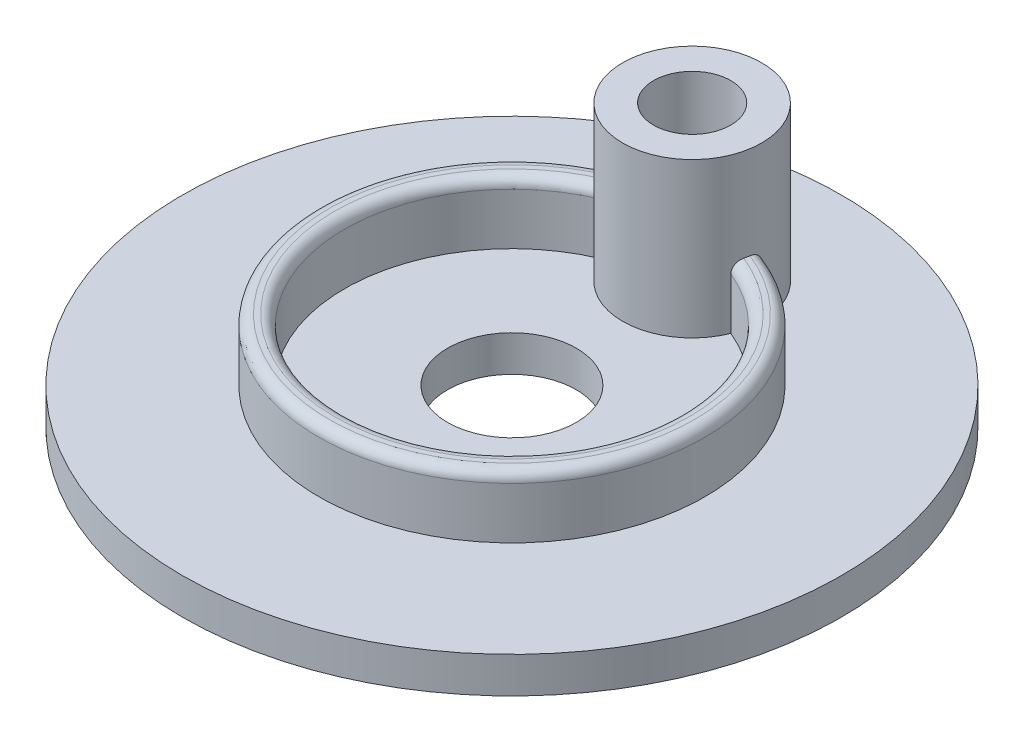
SolidWorks part; units mm, degrees
ref_plane "Front Plane" through (0, 0, 0) normal (0, 0, 1) x (1, 0, 0)
ref_plane "Top Plane" through (0, 0, 0) normal (0, 1, 0) x (1, 0, 0)
ref_plane "Right Plane" through (0, 0, 0) normal (1, 0, 0) x (0, 0, -1)
sketch "Sketch2" plane through (0, 0, 0) normal (0, 1, 0) x (1, 0, 0)
  circle A0 centre (0, 0) radius 64
  dimension "D1" = 128
extrude "Boss-Extrude1" add sketch "Sketch2" along normal blind 7
sketch "Sketch3" plane through (0, 7, 0) normal (0, 1, 0) x (1, 0, 0)
  circle A0 centre (0, 0) radius 37.5
  circle A1 centre (0, 0) radius 32.5
  dimension "D1" = 75
  dimension "D2" = 5
extrude "Boss-Extrude2" add sketch "Sketch3" along normal blind 12
sketch "Sketch4" plane through (0, 7, 0) normal (0, 1, 0) x (1, 0, 0)
  circle A0 centre (0, 0) radius 12.5
  dimension "D1" = 25
extrude "Cut-Extrude1" cut sketch "Sketch4" against normal through all
fillet "Fillet1" radius 2 2 edges at (0, 19, 32.5) (0, 19, 37.5)
sketch "Sketch5" plane through (0, 7, 0) normal (0, 1, 0) x (1, 0, 0)
  line L0 (0, 0) -> (0, 35)
  circle A0 centre (0, 35) radius 13.5
  dimension "D1" = 27
  dimension "D2" = 35
extrude "Boss-Extrude3" add sketch "Sketch5" along normal blind 30 contours A0
sketch "Sketch7" plane through (0, 37, 0) normal (0, 1, 0) x (1, 0, 0)
  circle A0 centre (0, 35) radius 7.5
  dimension "D1" = 15
extrude "Cut-Extrude2" cut sketch "Sketch7" against normal through all
